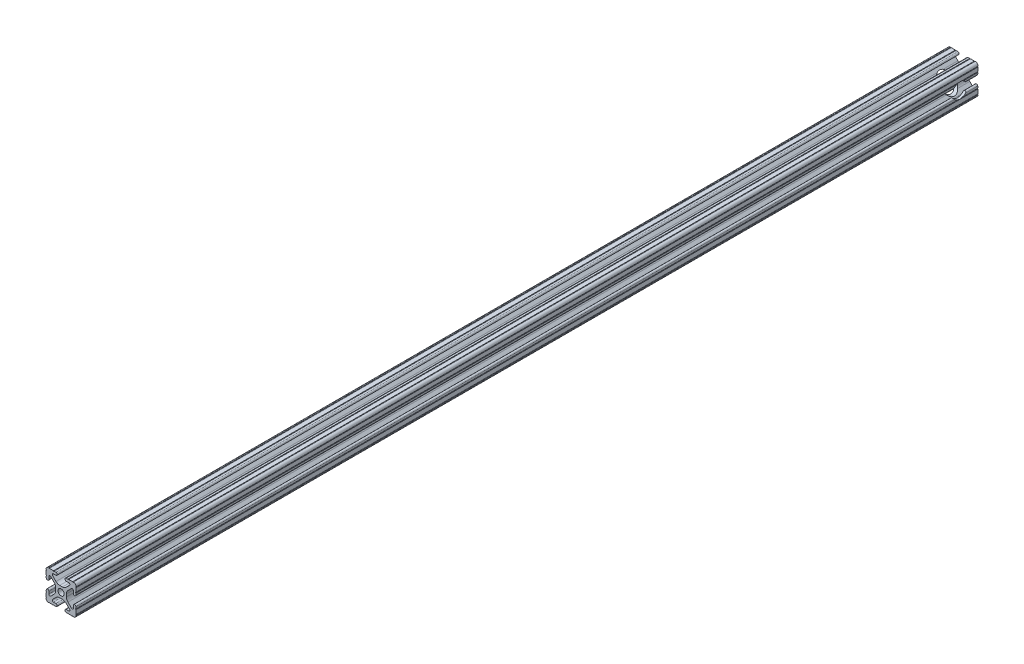
SolidWorks part; units mm, degrees
ref_plane "Front Plane" through (0, 0, 0) normal (0, 0, 1) x (1, 0, 0)
ref_plane "Top Plane" through (0, 0, 0) normal (0, 1, 0) x (1, 0, 0)
ref_plane "Right Plane" through (0, 0, 0) normal (1, 0, 0) x (0, 0, -1)
sketch "Sketch1" plane through (0, 0, 0) normal (0, 0, 1) x (1, 0, 0)
  line L0 (0, 12.7) -> (-12.7814, 12.7) construction
  line L1 (-4.5085, 0) -> (-4.5085, 2.9459)
  line L2 (-6.0437, 12.5461) -> (-10.0976, 12.6876) construction
  line L3 (-11.5616, 12.4229) -> (-4.3159, 12.1699) construction
  line L4 (-6.4364, 10.3486) -> (-6.3592, 12.5571) construction
  line L6 (-2.9459, 4.5085) -> (0, 4.5085)
  line L7 (0, 0) -> (0, 12.7) construction
  line L8 (0, 0) -> (-12.7814, 0) construction
  line L9 (0.7813, 0.7813) -> (-0.7813, -0.7813) construction
  line L10 (-2.9459, 4.5085) -> (-7.1484, 8.711)
  line L11 (-4.5085, 2.9459) -> (-8.711, 7.1484)
  line L13 (0, 0) -> (-12.7814, 12.7814) construction
  line L14 (-10.4131, 12.6987) -> (-4.3048, 12.4853)
  line L15 (-4.3048, 12.4853) -> (-4.382, 10.2769) construction
  line L16 (-4.382, 10.2769) -> (-6.4364, 10.3486)
  line L17 (-12.6987, 10.4131) -> (-12.4853, 4.3048)
  line L18 (-10.2769, 4.382) -> (-10.3486, 6.4364)
  circle A0 centre (0, 0) radius 2.6035
  arc A1 (-4.382, 10.2769) -> (-4.3048, 12.4853) centre (-4.3434, 11.3811) ccw
  arc A2 (-7.1484, 8.711) -> (-6.4364, 10.3486) centre (-6.4698, 9.3896) cw
  arc A3 (-8.711, 7.1484) -> (-10.3486, 6.4364) centre (-9.3896, 6.4698) ccw
  arc A4 (-10.2769, 4.382) -> (-12.4853, 4.3048) centre (-11.3811, 4.3434) cw
  arc A5 (-10.4131, 12.6987) -> (-12.6987, 10.4131) centre (-10.4902, 10.4902) ccw
  arc A6 (-10.4131, 12.6987) -> (-9.7821, 12.6766) centre (-10.0976, 12.6876) ccw
  arc A7 (-6.3592, 12.5571) -> (-5.7282, 12.5351) centre (-6.0437, 12.5461) ccw
  arc A8 (-12.5571, 6.3592) -> (-12.5351, 5.7282) centre (-12.5461, 6.0437) cw
  arc A9 (-12.6987, 10.4131) -> (-12.6766, 9.7821) centre (-12.6876, 10.0976) cw
  dimension "D1" = 5.207
  dimension "D5" = 14.859
  dimension "D9" = 2
  dimension "D2" = 25.4
  dimension "D12" = 0.6314
  dimension "D10" = 2.2098
  dimension "D3" = 9.017
  dimension "D4" = 9.017
  dimension "D6" = 25.4
  dimension "D7" = 6.477
  dimension "D8" = 2.2098
  dimension "D11" = 12.7
sketch "Sketch3" plane through (0, 0, 0) normal (0, 0, 1) x (1, 0, 0)
  line L0 (-2.9459, 4.5085) -> (0, 4.5085) construction
  line L1 (-2.9459, 4.5085) -> (-7.1484, 8.711) construction
  line L2 (-4.382, 10.2769) -> (-6.4364, 10.3486) construction
  line L3 (-10.4131, 12.6987) -> (-4.3048, 12.4853) construction
  line L4 (-4.5085, 0) -> (-4.5085, 2.9459) construction
  line L5 (-4.5085, 2.9459) -> (-8.711, 7.1484) construction
  line L6 (-10.2769, 4.382) -> (-10.3486, 6.4364) construction
  line L7 (-12.6987, 10.4131) -> (-12.4853, 4.3048) construction
  line L8 (-1.1153, 4.5085) -> (1.1153, 4.5085)
  line L9 (-4.2404, 5.803) -> (-7.1484, 8.711)
  line L10 (-4.382, 10.2769) -> (-6.4364, 10.3486)
  line L11 (-9.7821, 12.6766) -> (-6.3592, 12.5571)
  line L12 (-4.5085, -1.1153) -> (-4.5085, 1.1153)
  line L13 (-5.803, 4.2404) -> (-8.711, 7.1484)
  line L14 (-10.2769, 4.382) -> (-10.3486, 6.4364)
  line L15 (-12.6766, 9.7821) -> (-12.5571, 6.3592)
  line L16 (-5.7282, 12.5351) -> (-4.3048, 12.4853)
  line L17 (-12.5351, 5.7282) -> (-12.4853, 4.3048)
  line L18 (0, 0) -> (0, 12.7) construction
  line L19 (0, 0) -> (-12.7814, 0) construction
  line L20 (12.5351, 5.7282) -> (12.4853, 4.3048)
  line L21 (5.7282, 12.5351) -> (4.3048, 12.4853)
  line L22 (12.6766, 9.7821) -> (12.5571, 6.3592)
  line L23 (10.2769, 4.382) -> (10.3486, 6.4364)
  line L24 (5.803, 4.2404) -> (8.711, 7.1484)
  line L25 (4.5085, -1.1153) -> (4.5085, 1.1153)
  line L26 (9.7821, 12.6766) -> (6.3592, 12.5571)
  line L27 (4.382, 10.2769) -> (6.4364, 10.3486)
  line L28 (4.2404, 5.803) -> (7.1484, 8.711)
  line L29 (4.2404, -5.803) -> (7.1484, -8.711)
  line L30 (4.382, -10.2769) -> (6.4364, -10.3486)
  line L31 (9.7821, -12.6766) -> (6.3592, -12.5571)
  line L32 (5.803, -4.2404) -> (8.711, -7.1484)
  line L33 (10.2769, -4.382) -> (10.3486, -6.4364)
  line L34 (12.6766, -9.7821) -> (12.5571, -6.3592)
  line L35 (5.7282, -12.5351) -> (4.3048, -12.4853)
  line L36 (12.5351, -5.7282) -> (12.4853, -4.3048)
  line L37 (-12.5351, -5.7282) -> (-12.4853, -4.3048)
  line L38 (-5.7282, -12.5351) -> (-4.3048, -12.4853)
  line L39 (-12.6766, -9.7821) -> (-12.5571, -6.3592)
  line L40 (-10.2769, -4.382) -> (-10.3486, -6.4364)
  line L41 (-5.803, -4.2404) -> (-8.711, -7.1484)
  line L42 (-9.7821, -12.6766) -> (-6.3592, -12.5571)
  line L43 (-4.382, -10.2769) -> (-6.4364, -10.3486)
  line L44 (-4.2404, -5.803) -> (-7.1484, -8.711)
  line L45 (-1.1153, -4.5085) -> (1.1153, -4.5085)
  arc A0 (-10.4131, 12.6987) -> (-9.7821, 12.6766) centre (-10.0976, 12.6876) ccw construction
  arc A1 (-6.4364, 10.3486) -> (-7.1484, 8.711) centre (-6.4698, 9.3896) ccw construction
  arc A2 (-4.382, 10.2769) -> (-4.3048, 12.4853) centre (-4.3434, 11.3811) ccw construction
  arc A3 (-8.711, 7.1484) -> (-10.3486, 6.4364) centre (-9.3896, 6.4698) ccw construction
  arc A4 (-12.4853, 4.3048) -> (-10.2769, 4.382) centre (-11.3811, 4.3434) ccw construction
  arc A5 (-6.3592, 12.5571) -> (-5.7282, 12.5351) centre (-6.0437, 12.5461) ccw construction
  arc A6 (-10.4131, 12.6987) -> (-12.6987, 10.4131) centre (-10.4902, 10.4902) ccw construction
  arc A7 (-12.6766, 9.7821) -> (-12.6987, 10.4131) centre (-12.6876, 10.0976) ccw construction
  arc A8 (-12.5351, 5.7282) -> (-12.5571, 6.3592) centre (-12.5461, 6.0437) ccw construction
  arc A9 (-10.4131, 12.6987) -> (-9.7821, 12.6766) centre (-10.0976, 12.6876) ccw
  arc A10 (-6.4364, 10.3486) -> (-7.1484, 8.711) centre (-6.4698, 9.3896) ccw
  arc A11 (-4.382, 10.2769) -> (-4.3048, 12.4853) centre (-4.3434, 11.3811) ccw
  arc A12 (-8.711, 7.1484) -> (-10.3486, 6.4364) centre (-9.3896, 6.4698) ccw
  arc A13 (-12.4853, 4.3048) -> (-10.2769, 4.382) centre (-11.3811, 4.3434) ccw
  arc A14 (-6.3592, 12.5571) -> (-5.7282, 12.5351) centre (-6.0437, 12.5461) ccw
  arc A15 (-10.4131, 12.6987) -> (-12.6987, 10.4131) centre (-10.4902, 10.4902) ccw
  arc A16 (-12.6766, 9.7821) -> (-12.6987, 10.4131) centre (-12.6876, 10.0976) ccw
  arc A17 (-12.5351, 5.7282) -> (-12.5571, 6.3592) centre (-12.5461, 6.0437) ccw
  arc A18 (-1.1153, 4.5085) -> (-4.2404, 5.803) centre (-1.1153, 8.9281) cw
  arc A19 (4.5085, 1.1153) -> (5.803, 4.2404) centre (8.9281, 1.1153) cw
  arc A20 (1.1153, 4.5085) -> (4.2404, 5.803) centre (1.1153, 8.9281) ccw
  arc A21 (-4.5085, 1.1153) -> (-5.803, 4.2404) centre (-8.9281, 1.1153) ccw
  arc A22 (12.5351, 5.7282) -> (12.5571, 6.3592) centre (12.5461, 6.0437) cw
  arc A23 (12.6766, 9.7821) -> (12.6987, 10.4131) centre (12.6876, 10.0976) cw
  arc A24 (10.4131, 12.6987) -> (12.6987, 10.4131) centre (10.4902, 10.4902) cw
  arc A25 (6.3592, 12.5571) -> (5.7282, 12.5351) centre (6.0437, 12.5461) cw
  arc A26 (12.4853, 4.3048) -> (10.2769, 4.382) centre (11.3811, 4.3434) cw
  arc A27 (8.711, 7.1484) -> (10.3486, 6.4364) centre (9.3896, 6.4698) cw
  arc A28 (4.382, 10.2769) -> (4.3048, 12.4853) centre (4.3434, 11.3811) cw
  arc A29 (6.4364, 10.3486) -> (7.1484, 8.711) centre (6.4698, 9.3896) cw
  arc A30 (10.4131, 12.6987) -> (9.7821, 12.6766) centre (10.0976, 12.6876) cw
  arc A31 (10.4131, -12.6987) -> (9.7821, -12.6766) centre (10.0976, -12.6876) ccw
  arc A32 (6.4364, -10.3486) -> (7.1484, -8.711) centre (6.4698, -9.3896) ccw
  arc A33 (4.382, -10.2769) -> (4.3048, -12.4853) centre (4.3434, -11.3811) ccw
  arc A34 (8.711, -7.1484) -> (10.3486, -6.4364) centre (9.3896, -6.4698) ccw
  arc A35 (12.4853, -4.3048) -> (10.2769, -4.382) centre (11.3811, -4.3434) ccw
  arc A36 (6.3592, -12.5571) -> (5.7282, -12.5351) centre (6.0437, -12.5461) ccw
  arc A37 (10.4131, -12.6987) -> (12.6987, -10.4131) centre (10.4902, -10.4902) ccw
  arc A38 (12.6766, -9.7821) -> (12.6987, -10.4131) centre (12.6876, -10.0976) ccw
  arc A39 (12.5351, -5.7282) -> (12.5571, -6.3592) centre (12.5461, -6.0437) ccw
  arc A40 (-4.5085, -1.1153) -> (-5.803, -4.2404) centre (-8.9281, -1.1153) cw
  arc A41 (1.1153, -4.5085) -> (4.2404, -5.803) centre (1.1153, -8.9281) cw
  arc A42 (4.5085, -1.1153) -> (5.803, -4.2404) centre (8.9281, -1.1153) ccw
  arc A43 (-1.1153, -4.5085) -> (-4.2404, -5.803) centre (-1.1153, -8.9281) ccw
  arc A44 (-12.5351, -5.7282) -> (-12.5571, -6.3592) centre (-12.5461, -6.0437) cw
  arc A45 (-12.6766, -9.7821) -> (-12.6987, -10.4131) centre (-12.6876, -10.0976) cw
  arc A46 (-10.4131, -12.6987) -> (-12.6987, -10.4131) centre (-10.4902, -10.4902) cw
  arc A47 (-6.3592, -12.5571) -> (-5.7282, -12.5351) centre (-6.0437, -12.5461) cw
  arc A48 (-12.4853, -4.3048) -> (-10.2769, -4.382) centre (-11.3811, -4.3434) cw
  arc A49 (-8.711, -7.1484) -> (-10.3486, -6.4364) centre (-9.3896, -6.4698) cw
  arc A50 (-4.382, -10.2769) -> (-4.3048, -12.4853) centre (-4.3434, -11.3811) cw
  arc A51 (-6.4364, -10.3486) -> (-7.1484, -8.711) centre (-6.4698, -9.3896) cw
  arc A52 (-10.4131, -12.6987) -> (-9.7821, -12.6766) centre (-10.0976, -12.6876) cw
  circle A53 centre (0, 0) radius 2.6035 construction
  circle A54 centre (0, 0) radius 2.6035
  point P135 (4.5085, 0)
  dimension "D2" = 4.4196
extrude "Extrude1" add sketch "Sketch3" along normal mid plane 760
ref_plane "Plane1" through (12.4853, 4.3048, 380) normal (0.0349, 0.9994, 0) x (0.9994, -0.0349, 0)
sketch "Sketch5" plane through (4.5085, 0, 0) normal (1, 0, 0) x (0, 0, -1)
  line L1 (380, -1.1153) -> (380, 1.1153) construction
  circle A0 centre (365, 0) radius 6.35
  dimension "D1" = 12.7
  dimension "D2" = 15
extrude "Cut-Extrude2" cut sketch "Sketch5" against normal through all and the other way through all
equation "\"D10@Sketch1\" = \"D8@Sketch1\""
equation "\"D11@Sketch1\" = \"D6@Sketch1\"/2"
equation "\"D12@Sketch1\" = \"D8@Sketch1\"/3.5"
equation "\"D2@Sketch3\" = \"D8@Sketch1\"*2"
